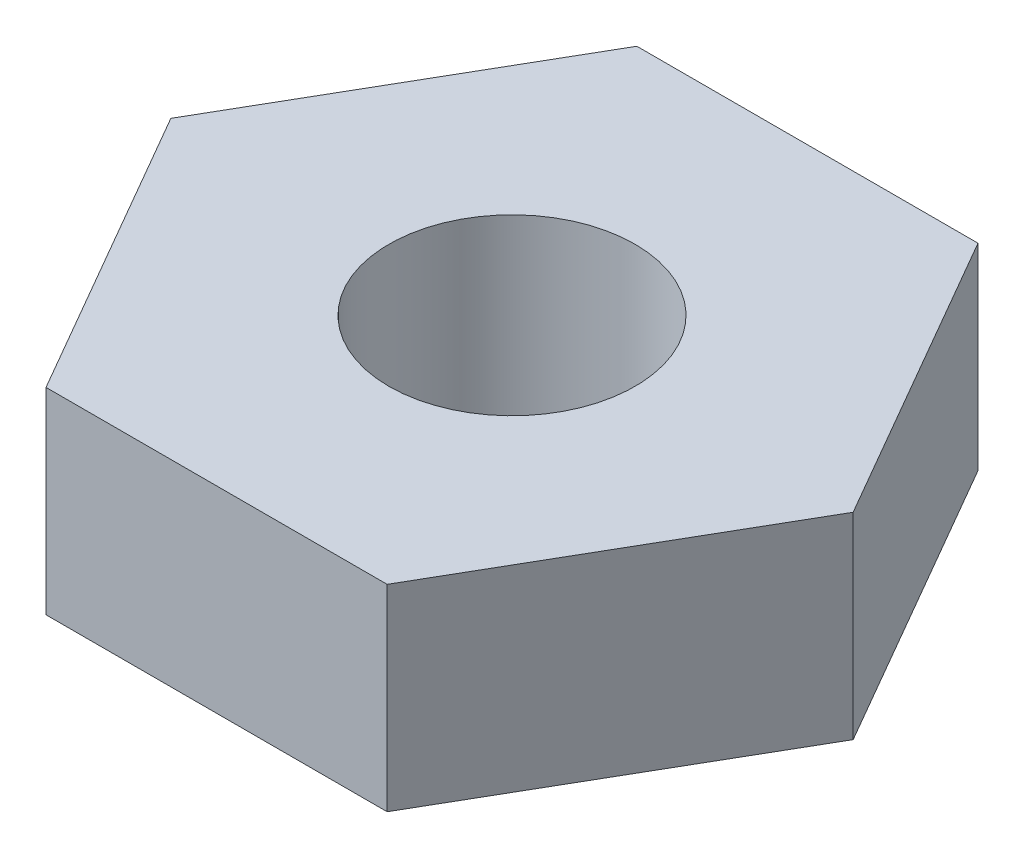
SolidWorks part; units mm, degrees
material "201 Annealed Stainless Steel (SS)"
ref_plane "Front Plane" through (0, 0, 0) normal (0, 0, 1) x (1, 0, 0)
ref_plane "Top Plane" through (0, 0, 0) normal (0, 1, 0) x (1, 0, 0)
ref_plane "Right Plane" through (0, 0, 0) normal (1, 0, 0) x (0, 0, -1)
sketch "Sketch1" plane through (0, 0, 0) normal (0, 1, 0) x (1, 0, 0)
  line L1 (2.7713, 0) -> (1.3856, 2.4)
  line L2 (1.3856, 2.4) -> (-1.3856, 2.4)
  line L3 (-1.3856, 2.4) -> (-2.7713, 0)
  line L4 (-2.7713, 0) -> (-1.3856, -2.4)
  line L5 (-1.3856, -2.4) -> (1.3856, -2.4)
  line L6 (1.3856, -2.4) -> (2.7713, 0)
  circle A0 centre (0, 0) radius 2.4 construction
  circle A1 centre (0, 0) radius 1
  dimension "D1" = 4.8
  dimension "D2" = 2
extrude "Extrude1" add sketch "Sketch1" along normal blind 1.6
